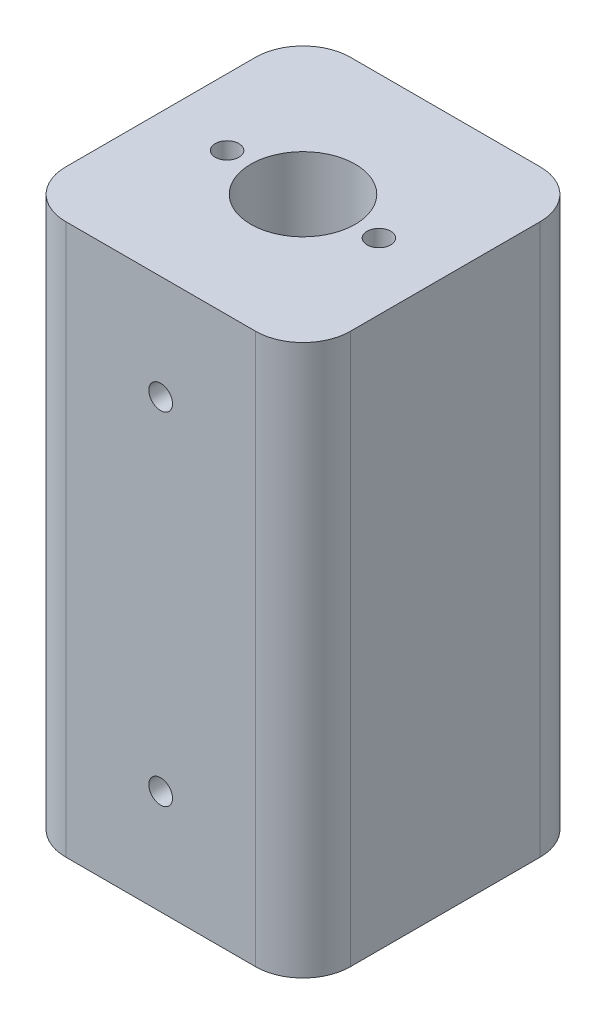
SolidWorks part; units mm, degrees
ref_plane "Front Plane" through (0, 0, 0) normal (0, 0, 1) x (1, 0, 0)
ref_plane "Top Plane" through (0, 0, 0) normal (0, 1, 0) x (1, 0, 0)
ref_plane "Right Plane" through (0, 0, 0) normal (1, 0, 0) x (0, 0, -1)
sketch "Sketch1" plane through (0, 0, 0) normal (0, 1, 0) x (1, 0, 0)
  line L0 (-40.8567, 0) -> (48.8389, 0) construction
  line L1 (0, 25.9431) -> (0, -21.8825) construction
  line L3 (-15, 15) -> (15, 15)
  line L4 (-15, 15) -> (-15, -15)
  line L5 (-15, -15) -> (15, -15)
  line L6 (15, 15) -> (15, -15)
  line L7 (-15, 15) -> (15, -15) construction
  line L8 (-15, -15) -> (15, 15) construction
  point P5 (0, 0)
  dimension "D1" = 30
  dimension "D2" = 30
extrude "Boss-Extrude1" add sketch "Sketch1" along normal blind 58
sketch "Sketch2" plane through (0, 58, 0) normal (0, 1, 0) x (1, 0, 0)
  circle A0 centre (0, 0) radius 5.5
  circle A1 centre (8, 0) radius 1.25
  circle A2 centre (-8, 0) radius 1.25
  dimension "D1" = 11
  dimension "D2" = 2.5
  dimension "D3" = 16
  dimension "D4" = 8
  dimension "D5" = 8
extrude "Cut-Extrude1" cut sketch "Sketch2" against normal blind 10
sketch "Sketch3" plane through (0, 48, 0) normal (0, 1, 0) x (1, 0, 0)
  circle A0 centre (0, 0) radius 5.5
  dimension "D1" = 11
extrude "Cut-Extrude2" cut sketch "Sketch3" against normal through all
sketch "Sketch4" plane through (0, 0, 15) normal (0, 0, 1) x (1, 0, 0)
  line L0 (-15, 58) -> (15, 58) construction
  line L1 (15, 58) -> (15, 0) construction
  line L2 (-15, 0) -> (15, 0) construction
  circle A0 centre (0, 47) radius 1.25
  circle A2 centre (0, 11) radius 1.25
  dimension "D1" = 36
  dimension "D2" = 2.5
  dimension "D3" = 11
  dimension "D4" = 15
  dimension "D5" = 11
extrude "Cut-Extrude3" cut sketch "Sketch4" against normal blind 8
mirror "Mirror1" about plane through (0, 0, 0) normal (0, 0, 1) of "Cut-Extrude3"
fillet "Fillet1" radius 5 4 edges at (15, 29, -15) (15, 29, 15) (-15, 29, 15) (-15, 29, -15)
